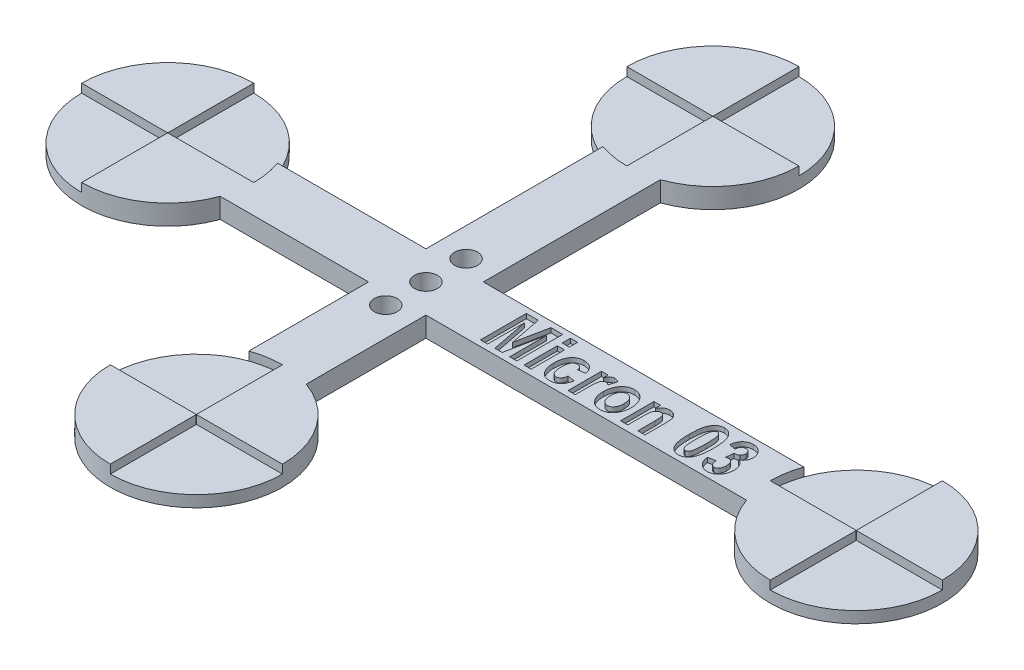
SolidWorks part; units mm, degrees
ref_plane "Front Plane" through (0, 0, 0) normal (0, 0, 1) x (1, 0, 0)
ref_plane "Top Plane" through (0, 0, 0) normal (0, 1, 0) x (1, 0, 0)
ref_plane "Right Plane" through (0, 0, 0) normal (1, 0, 0) x (0, 0, -1)
sketch "Sketch1" plane through (0, 0, 0) normal (0, 1, 0) x (1, 0, 0)
  line L0 (0, 0) -> (120, 0) construction
  line L1 (45, -40) -> (45, 50) construction
  line L2 (40, 35.8579) -> (40, 5)
  line L3 (50, -25.8579) -> (50, -5)
  line L4 (14.1421, 5) -> (40, 5)
  line L5 (105.8579, -5) -> (50, -5)
  line L6 (50, 5) -> (105.8579, 5)
  line L7 (40, -5) -> (40, -25.8579)
  line L8 (40, -5) -> (14.1421, -5)
  line L9 (50, 5) -> (50, 35.8579)
  arc A0 (14.1421, 5) -> (14.1421, -5) centre (0, 0) ccw
  arc A1 (105.8579, -5) -> (105.8579, 5) centre (120, 0) ccw
  arc A2 (50, 35.8579) -> (40, 35.8579) centre (45, 50) ccw
  arc A3 (40, -25.8579) -> (50, -25.8579) centre (45, -40) ccw
  dimension "D1" = 30
  dimension "D3" = 30
  dimension "D5" = 30
  dimension "D6" = 30
  dimension "D2" = 120
  dimension "D4" = 45
  dimension "D7" = 90
  dimension "D8" = 50
  dimension "D9" = 5
  dimension "D10" = 5
  dimension "D11" = 5
  dimension "D12" = 5
extrude "Boss-Extrude1" add sketch "Sketch1" along normal blind 3.5
sketch "Sketch2" plane through (0, 3.5, 0) normal (0, 1, 0) x (1, 0, 0)
  line L0 (-15, 0) -> (-0.05, 0)
  line L1 (45, 65) -> (45, 50.05)
  line L2 (30, 50) -> (44.95, 50)
  line L3 (120, 15) -> (120, 0.05)
  line L4 (0, 15) -> (0, 0.05)
  line L5 (30, -40) -> (44.95, -40)
  line L6 (45.05, 50) -> (60, 50)
  line L7 (45, 49.95) -> (45, 35)
  line L8 (45, -40.05) -> (45, -55)
  line L9 (45.05, -40) -> (60, -40)
  line L10 (0, -0.05) -> (0, -15)
  line L11 (0.05, 0) -> (15, 0)
  line L12 (120, -0.05) -> (120, -15)
  line L13 (120.05, 0) -> (135, 0)
  line L14 (105, 0) -> (119.95, 0)
  line L15 (45, -25) -> (45, -39.95)
  arc A0 (30, 50) -> (45, 35) centre (45, 50) ccw
  arc A1 (-15, 0) -> (0, -15) centre (0, 0) ccw
  arc A2 (45, -55) -> (60, -40) centre (45, -40) ccw
  arc A3 (120, 15) -> (105, 0) centre (120, 0) ccw
  arc A4 (0, 0.05) -> (-0.05, 0) centre (0, 0) ccw
  arc A5 (45, 49.95) -> (45.05, 50) centre (45, 50) ccw
  arc A6 (119.95, 0) -> (120, -0.05) centre (120, 0) ccw
  arc A7 (44.95, -40) -> (45, -40.05) centre (45, -40) ccw
  arc A8 (45, 50.05) -> (44.95, 50) centre (45, 50) ccw
  arc A9 (60, 50) -> (45, 65) centre (45, 50) ccw
  arc A10 (45.05, -40) -> (45, -39.95) centre (45, -40) ccw
  arc A11 (45, -25) -> (30, -40) centre (45, -40) ccw
  arc A12 (0, -0.05) -> (0.05, 0) centre (0, 0) ccw
  arc A13 (15, 0) -> (0, 15) centre (0, 0) ccw
  arc A14 (120.05, 0) -> (120, 0.05) centre (120, 0) ccw
  arc A15 (120, -15) -> (135, 0) centre (120, 0) ccw
  arc A16 (40, -25.8579) -> (50, -25.8579) centre (45, -40) ccw construction
  arc A17 (50, 35.8579) -> (40, 35.8579) centre (45, 50) ccw construction
  dimension "D1" = 0.1
  dimension "D2" = 0.1
  dimension "D3" = 0.1
  dimension "D4" = 0.1
extrude "Cut-Extrude1" cut sketch "Sketch2" against normal blind 1.5
sketch "Sketch3" plane through (0, 3.5, 0) normal (0, 1, 0) x (1, 0, 0)
  line L0 (55.4289, -4) -> (100.4289, -4) construction
  line L1 (50, -5) -> (105.8579, -5) construction
  text T0 "<b>Micron 03</b>" font "Arial Narrow" height 8
  point P4 (77.9289, -4)
  point P5 (77.9289, -5)
  dimension "D1" = 45
  dimension "D2" = 1
extrude "Cut-Extrude2" cut sketch "Sketch3" against normal blind 0.8
sketch "Sketch4" plane through (0, 3.5, 0) normal (0, 1, 0) x (1, 0, 0)
  line L0 (45, 7) -> (45, -7) construction
  line L1 (0.05, 0) -> (15, 0) construction
  line L2 (45, -39.95) -> (45, -25) construction
  circle A0 centre (45, 0) radius 2
  circle A1 centre (45, 7) radius 2
  circle A2 centre (45, -7) radius 2
  point P4 (45, 0)
  dimension "D1" = 4
  dimension "D3" = 4
  dimension "D4" = 4
  dimension "D2" = 14
extrude "Cut-Extrude3" cut sketch "Sketch4" against normal through all
